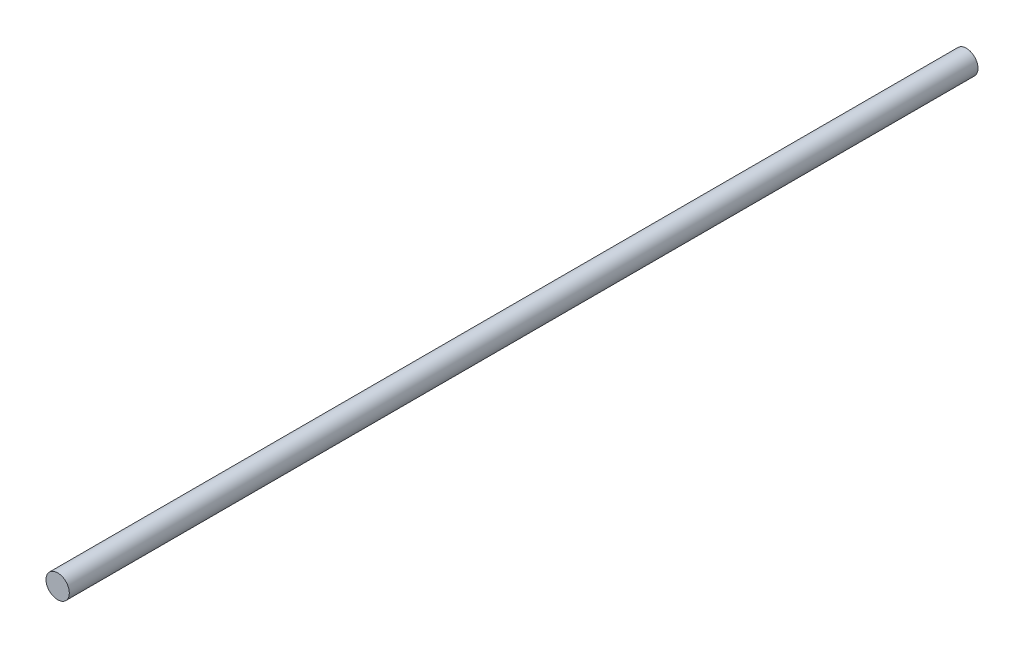
SolidWorks part; units mm, degrees
ref_plane "Front Plane" through (0, 0, 0) normal (0, 0, 1) x (1, 0, 0)
ref_plane "Top Plane" through (0, 0, 0) normal (0, 1, 0) x (1, 0, 0)
ref_plane "Right Plane" through (0, 0, 0) normal (1, 0, 0) x (0, 0, -1)
sketch "Sketch1" plane through (0, 0, 0) normal (0, 0, 1) x (1, 0, 0)
  circle A0 centre (0, 0) radius 4
  dimension "D1" = 8
extrude "Boss-Extrude1" add sketch "Sketch1" along normal blind 311.5
move or copy body "Body-Move/Copy1" [suppressed] bodies to move or copy 101
